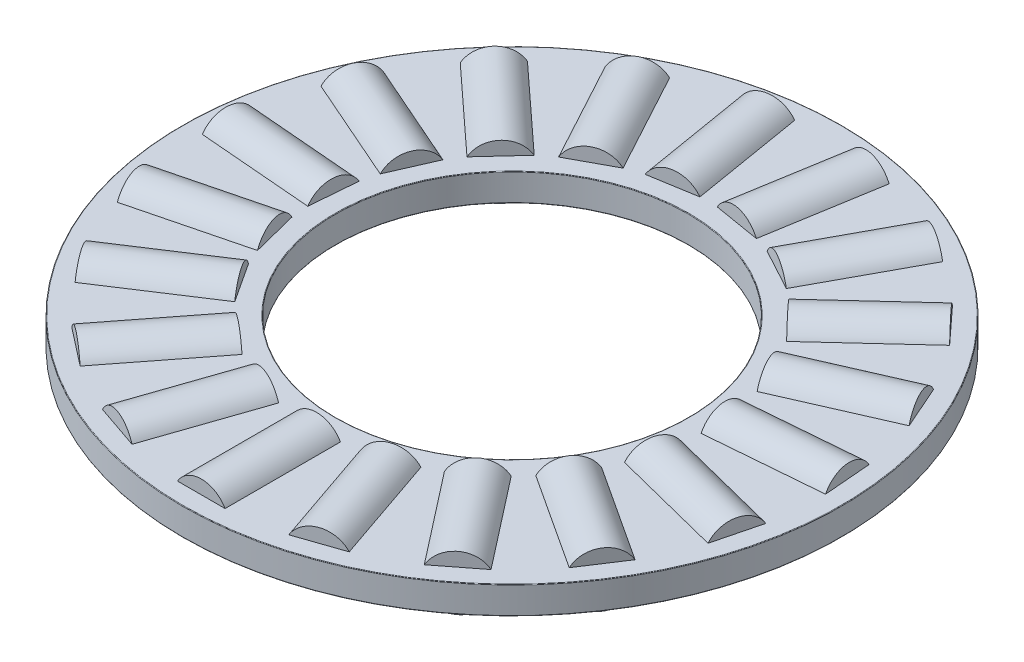
SolidWorks part; units mm, degrees
ref_plane "Front Plane" through (0, 0, 0) normal (0, 0, 1) x (1, 0, 0)
ref_plane "Top Plane" through (0, 0, 0) normal (0, 1, 0) x (1, 0, 0)
ref_plane "Right Plane" through (0, 0, 0) normal (1, 0, 0) x (0, 0, -1)
sketch "Sketch1" plane through (0, 0, 0) normal (1, 0, 0) x (0, 0, -1)
  line L0 (-11.9062, 0) -> (11.9062, 0) construction
  line L1 (0, -0.9922) -> (0, 0.9922) construction
  line L2 (-11.9063, 0.4961) -> (-6.3754, 0.4961)
  line L3 (-11.9063, 0.4961) -> (-11.9063, -0.4961)
  line L4 (-11.9063, -0.4961) -> (-6.3754, -0.4961)
  line L5 (-6.3754, 0.4961) -> (-6.3754, -0.4961)
  line L7 (-9.1408, 0.9922) -> (-9.1408, 0.4961) construction
  line L8 (-11.2244, 0.9922) -> (-7.0572, 0.9922) construction
  line L9 (-11.2244, 0.9922) -> (-11.2244, -0.9922) construction
  line L10 (-11.2244, -0.9922) -> (-7.0572, -0.9922) construction
  line L11 (-7.0572, 0.9922) -> (-7.0572, -0.9922) construction
  point P16 (-11.2244, 0)
  dimension "OD" = 23.8125
  dimension "Shaft Dia" = 12.7508
  dimension "Th" = 1.9844
  dimension "D2" = 0.9922
  dimension "D1" = 4.1672
  dimension "D3" = 5.5309
revolve "Revolve1" add sketch "Sketch1" angle 360 about L1
sketch "Sketch3" plane through (0, 0, 0) normal (1, 0, 0) x (0, 0, -1)
  line L0 (-11.2244, 0.9922) -> (-11.2244, -0.9922) construction
  line L1 (-11.2244, 0) -> (-7.0572, 0)
  line L2 (-11.2244, 0) -> (-11.2244, 0.9922)
  line L3 (-11.2244, 0.9922) -> (-7.0572, 0.9922)
  line L4 (-7.0572, 0) -> (-7.0572, 0.9922)
revolve "Cut-Revolve1" cut sketch "Sketch3" angle 360 about L1
sketch "Sketch2" plane through (0, 0, 0) normal (1, 0, 0) x (0, 0, -1)
  line L1 (-11.2244, 0) -> (-7.0572, 0)
  line L2 (-11.2244, 0) -> (-11.2244, 0.9922)
  line L3 (-11.2244, 0.9922) -> (-7.0572, 0.9922)
  line L4 (-7.0572, 0) -> (-7.0572, 0.9922)
revolve "Revolve2" add sketch "Sketch2" angle 360 about L1
ref_axis "Axis1" through (0, 0.9922, 0) along (0, -1, 0)
pattern_circular "CirPattern1" count 19 every 18.947 about axis through (0, 0.9922, 0) along (0, -1, 0) of bodies 187 411
pattern_circular "CirPattern2" count 19 every 18.947 about axis through (0, 0, 0) along (0, 1, 0) of "Cut-Revolve1"
sketch "Sketch4" [suppressed] plane through (0, 0, 0) normal (1, 0, 0) x (0, 0, -1)
  line L0 (-11.9063, 0.4961) -> (-11.9063, -0.4961) construction
  line L1 (-11.9062, 9.1091) -> (-6.35, 9.1091)
  line L2 (-11.9062, 9.1091) -> (-11.9062, 9.9219)
  line L3 (-11.9062, 9.9219) -> (-6.35, 9.9219)
  line L4 (-6.35, 9.1091) -> (-6.35, 9.9219)
  line L5 (-11.9062, -9.9219) -> (-6.3754, -9.9219)
  line L6 (-11.9062, -9.9219) -> (-11.9062, -9.1091)
  line L7 (-11.9062, -9.1091) -> (-6.3754, -9.1091)
  line L8 (-6.3754, -9.9219) -> (-6.3754, -9.1091)
  line L10 (-6.3754, 0.4961) -> (-6.3754, -0.4961) construction
  line L11 (0, 0) -> (-11.9062, 0) construction
  line L12 (-11.9062, 0) -> (11.9062, 0) construction
  line L13 (0, -0.9922) -> (0, 0.9922) construction
  dimension "Ht" = 19.8438
  dimension "Washer Th" = 0.8128
  dimension "Washer ID" = 12.7
  dimension "Washer OD" = 23.8125
fillet "Fillet2" radius 0.0198 4 edges at (0, -0.4961, -6.3754) (0, 0.4961, -6.3754) (0, -0.4961, -11.9063) (0, 0.4961, -11.9063)
equation "\"D2@Sketch1\"= \"Th@Sketch1\" * .5"
equation "\"Rollers@CirPattern1\"= \"OD@Sketch1\" * 20"
equation "\"Angle@CirPattern1\" = 360/\"Rollers@CirPattern1\""
equation "\"D1@CirPattern2\" = \"Rollers@CirPattern1\""
equation "\"D2@CirPattern2\" = \"Angle@CirPattern1\""
equation "\"Ht@Sketch4\" = \"Th@Sketch1\"*10"
